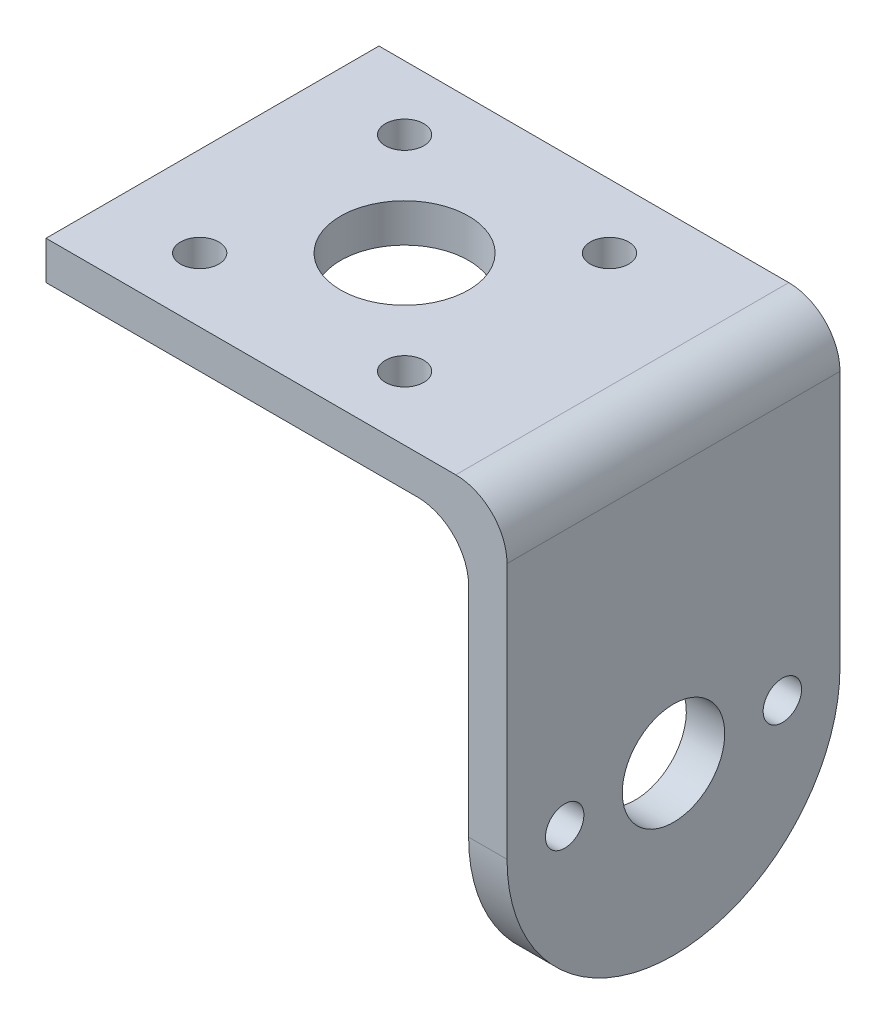
SolidWorks part; units mm, degrees
ref_plane "Front Plane" through (0, 0, 0) normal (0, 0, 1) x (1, 0, 0)
ref_plane "Top Plane" through (0, 0, 0) normal (0, 1, 0) x (1, 0, 0)
ref_plane "Right Plane" through (0, 0, 0) normal (1, 0, 0) x (0, 0, -1)
sketch "Sketch1" plane through (0, 0, 0) normal (0, 0, 1) x (1, 0, 0)
  line L0 (0, 0) -> (33, 0)
  line L1 (33, 0) -> (33, -34)
  line L2 (0, 3) -> (36, 3)
  line L3 (36, 3) -> (36, -34)
  line L4 (0, 3) -> (0, 0)
  line L5 (33, -34) -> (36, -34)
  dimension "D1" = 34
  dimension "D2" = 33
  dimension "D3" = 3
extrude "Boss-Extrude1" add sketch "Sketch1" along normal blind 26
sketch "Sketch2" plane through (36, 0, 0) normal (1, 0, 0) x (0, 0, -1)
  line L0 (-13, 3) -> (-13, -34) construction
  line L1 (-26, 3) -> (0, 3) construction
  line L2 (-26, -34) -> (0, -34) construction
  line L3 (0, -34) -> (0, 3) construction
  line L4 (-26, -21) -> (-26, -34)
  line L5 (-26, -34) -> (0, -34)
  line L6 (0, -34) -> (0, -21)
  line L7 (-21.5, -21) -> (-26, -21) construction
  line L8 (-4.5, -21) -> (0, -21) construction
  arc A0 (-26, -21) -> (0, -21) centre (-13, -21) ccw
  circle A1 centre (-13, -21) radius 4
  circle A2 centre (-4.5, -21) radius 1.5
  circle A3 centre (-21.5, -21) radius 1.5
  line M1 (0, -34) -> (0, 3)
  line M3 (-26, 3) -> (-26, -34)
  line M4 (-26, -34) -> (0, -34)
  dimension "D1" = 8
  dimension "D2" = 3
  dimension "D3" = 3
  dimension "D4" = 17
extrude "Cut-Extrude1" cut sketch "Sketch2" against normal blind 26 contours A0 M3 M4 | A0 L5 M1 | A2 | A1 | A3
fillet "Fillet1" radius 4 2 edges at (36, 3, 13) (33, 0, 13)
sketch "Sketch3" plane through (0, 3, 0) normal (0, 1, 0) x (1, 0, 0)
  line L0 (0, -13) -> (15, -13) construction
  line L1 (0, -26) -> (0, 0) construction
  line L2 (15, -13) -> (23, -21) construction
  line L3 (15, -13) -> (7, -21) construction
  line L4 (15, -13) -> (23, -5) construction
  line L5 (15, -13) -> (7, -5) construction
  circle A0 centre (15, -13) radius 5
  circle A1 centre (23, -21) radius 1.5
  circle A2 centre (23, -5) radius 1.5
  circle A3 centre (7, -5) radius 1.5
  circle A4 centre (7, -21) radius 1.5
  dimension "D1" = 3
  dimension "D2" = 10
  dimension "D3" = 16
  dimension "D4" = 15
extrude "Cut-Extrude2" cut sketch "Sketch3" against normal blind 26
